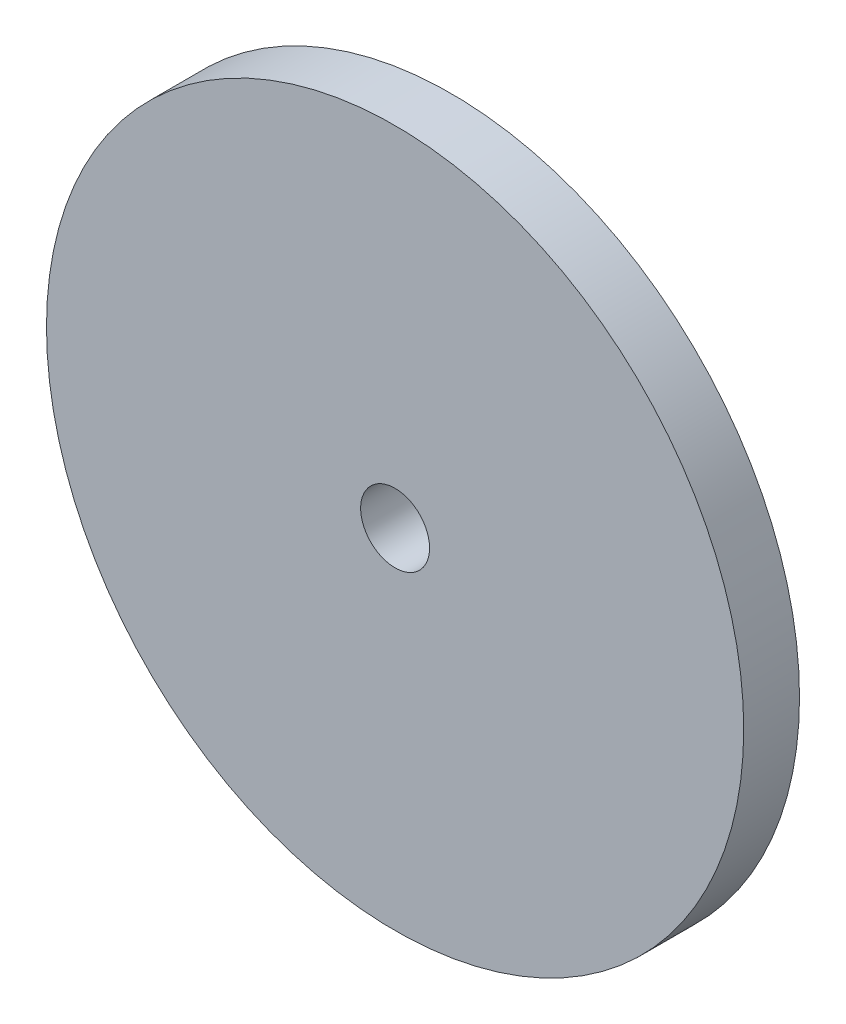
SolidWorks part; units mm, degrees
ref_plane "Front Plane" through (0, 0, 0) normal (0, 0, 1) x (1, 0, 0)
ref_plane "Top Plane" through (0, 0, 0) normal (0, 1, 0) x (1, 0, 0)
ref_plane "Right Plane" through (0, 0, 0) normal (1, 0, 0) x (0, 0, -1)
sketch "Sketch1" plane through (0, 0, 0) normal (1, 0, 0) x (0, 0, -1)
  line L0 (0, 0) -> (8.1994, 0) construction
  line L1 (0, 3.1369) -> (0, 31.75)
  line L2 (0, 31.75) -> (5.08, 31.75)
  line L3 (5.08, 31.75) -> (5.08, 3.1369)
  line L4 (5.08, 3.1369) -> (0, 3.1369)
  dimension "D1" = 6.2738
  dimension "D2" = 63.5
  dimension "D3" = 5.08
revolve "Revolve1" add sketch "Sketch1" angle 360 about L0
